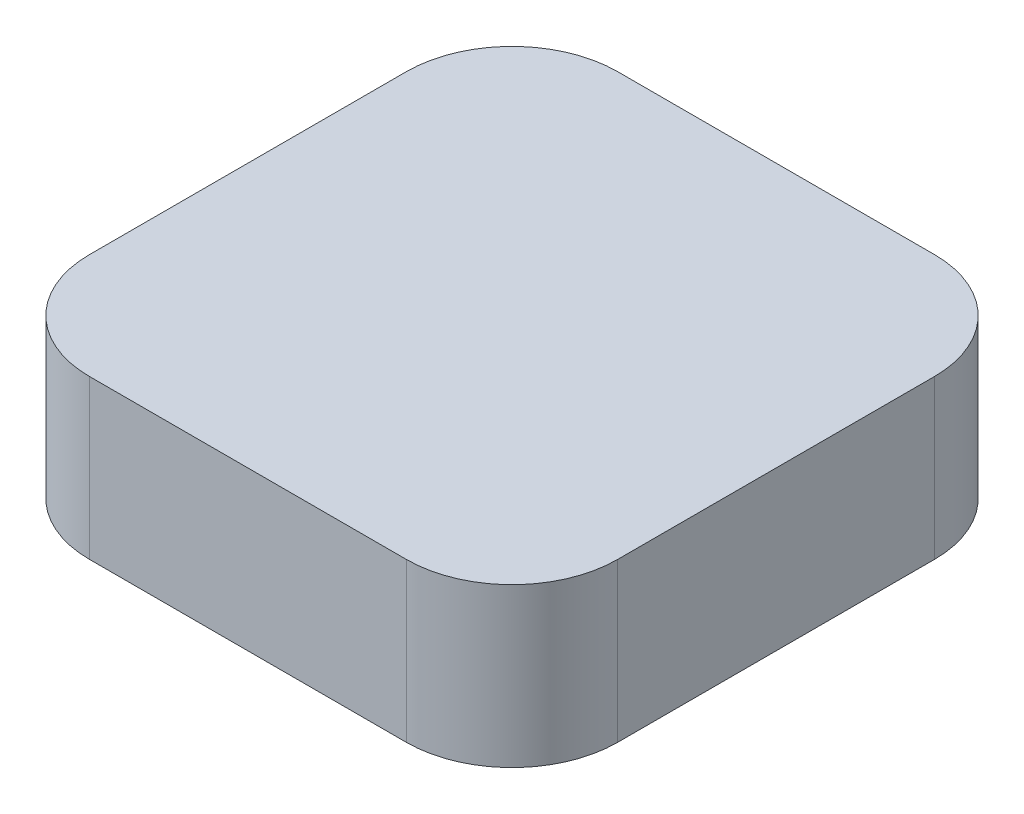
SolidWorks part; units mm, degrees
ref_plane "Front Plane" through (0, 0, 0) normal (0, 0, 1) x (1, 0, 0)
ref_plane "Top Plane" through (0, 0, 0) normal (0, 1, 0) x (1, 0, 0)
ref_plane "Right Plane" through (0, 0, 0) normal (1, 0, 0) x (0, 0, -1)
sketch "Sketch1" plane through (0, 0, 0) normal (0, 1, 0) x (1, 0, 0)
  line L1 (-2.5385, 3.5769) -> (3.4615, 3.5769)
  line L2 (-4.5385, 1.5769) -> (-4.5385, -4.4231)
  line L3 (-2.5385, -6.4231) -> (3.4615, -6.4231)
  line L4 (5.4615, 1.5769) -> (5.4615, -4.4231)
  arc A0 (-2.5385, -6.4231) -> (-4.5385, -4.4231) centre (-2.5385, -4.4231) cw
  arc A1 (5.4615, 1.5769) -> (3.4615, 3.5769) centre (3.4615, 1.5769) ccw
  arc A2 (3.4615, -6.4231) -> (5.4615, -4.4231) centre (3.4615, -4.4231) ccw
  arc A3 (-2.5385, 3.5769) -> (-4.5385, 1.5769) centre (-2.5385, 1.5769) ccw
  point P6 (-4.5385, -6.4231)
  point P9 (5.4615, 3.5769)
  point P14 (-4.5385, 3.5769)
  dimension "D3" = 2
  dimension "D1" = 10
  dimension "D2" = 10
extrude "Boss-Extrude1" add sketch "Sketch1" along normal blind 3
